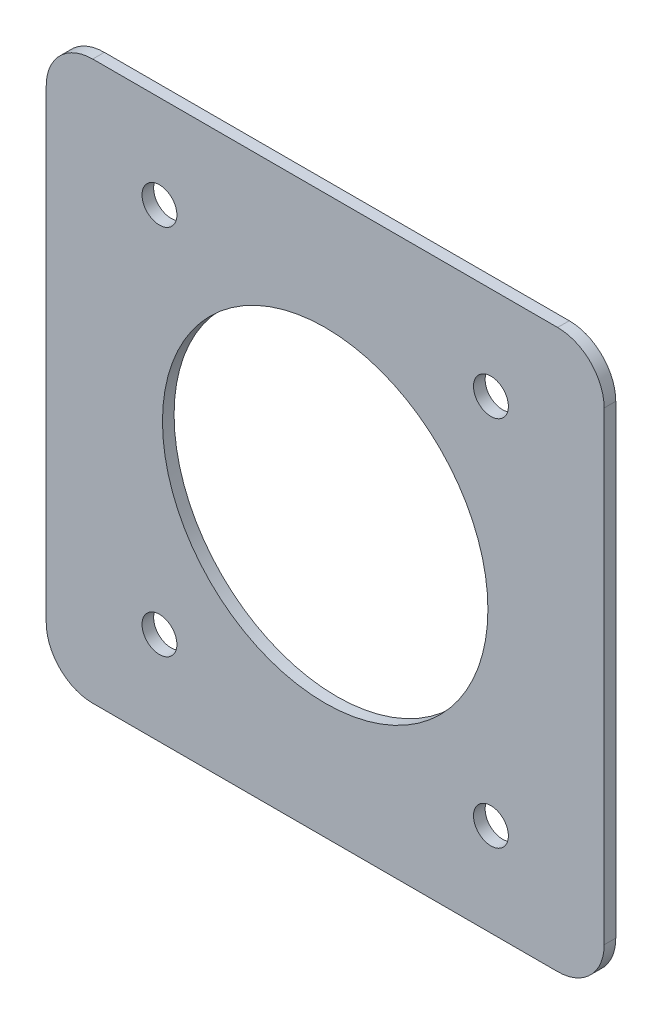
SolidWorks part; units mm, degrees
ref_plane "Front Plane" through (0, 0, 0) normal (0, 0, 1) x (1, 0, 0)
ref_plane "Top Plane" through (0, 0, 0) normal (0, 1, 0) x (1, 0, 0)
ref_plane "Right Plane" through (0, 0, 0) normal (1, 0, 0) x (0, 0, -1)
sketch "Sketch1" plane through (0, 0, 0) normal (0, 0, 1) x (1, 0, 0)
  line L10 (-212.7732, 125.0857) -> (-122.2222, 125.0857) construction
  line L11 (-230.9977, 150.4857) -> (-103.9977, 150.4857)
  line L12 (-243.6977, 137.7857) -> (-243.6977, 10.7857)
  line L13 (-230.9977, -1.9143) -> (-103.9977, -1.9143)
  line L14 (-91.2977, 137.7857) -> (-91.2977, 10.7857)
  line L15 (-167.4977, 150.4857) -> (-167.4977, 99.6857) construction
  line L17 (-243.6977, 74.2857) -> (-91.2977, 74.2857) construction
  circle A0 centre (-122.2222, 125.0857) radius 4.7625 construction
  circle A1 centre (-212.7732, 125.0857) radius 4.7625 construction
  circle A2 centre (-122.2222, 125.0857) radius 4.7625
  circle A3 centre (-212.7732, 125.0857) radius 4.7625
  circle A4 centre (-212.7732, 23.4857) radius 4.7625 construction
  circle A5 centre (-212.7732, 23.4857) radius 4.7625
  circle A6 centre (-122.2222, 23.4857) radius 4.7625 construction
  circle A7 centre (-122.2222, 23.4857) radius 4.7625
  arc A8 (-243.6977, 10.7857) -> (-230.9977, -1.9143) centre (-230.9977, 10.7857) ccw
  arc A9 (-103.9977, -1.9143) -> (-91.2977, 10.7857) centre (-103.9977, 10.7857) ccw
  arc A10 (-230.9977, 150.4857) -> (-243.6977, 137.7857) centre (-230.9977, 137.7857) ccw
  arc A11 (-103.9977, 150.4857) -> (-91.2977, 137.7857) centre (-103.9977, 137.7857) cw
  point P24 (-167.4977, 125.0857)
  point P25 (-243.6977, -1.9143)
  point P33 (-243.6977, 150.4857)
  dimension "D2" = 12.7
  dimension "D1" = 152.4
extrude "Boss-Extrude1" add sketch "Sketch1" along normal blind 3.175
sketch "Sketch2" plane through (0, 0, 3.175) normal (0, 0, 1) x (1, 0, 0)
  line L0 (-243.6977, 74.2857) -> (-91.2977, 74.2857) construction
  line L1 (-243.6977, 137.7857) -> (-243.6977, 10.7857) construction
  line L2 (-91.2977, 137.7857) -> (-91.2977, 10.7857) construction
  line L3 (-167.4977, -1.9143) -> (-167.4977, 150.4857) construction
  line L4 (-230.9977, -1.9143) -> (-103.9977, -1.9143) construction
  line L5 (-230.9977, 150.4857) -> (-103.9977, 150.4857) construction
  circle A0 centre (-167.4977, 74.2857) radius 44.45
  dimension "D1" = 88.9
extrude "Cut-Extrude1" cut sketch "Sketch2" against normal through all
